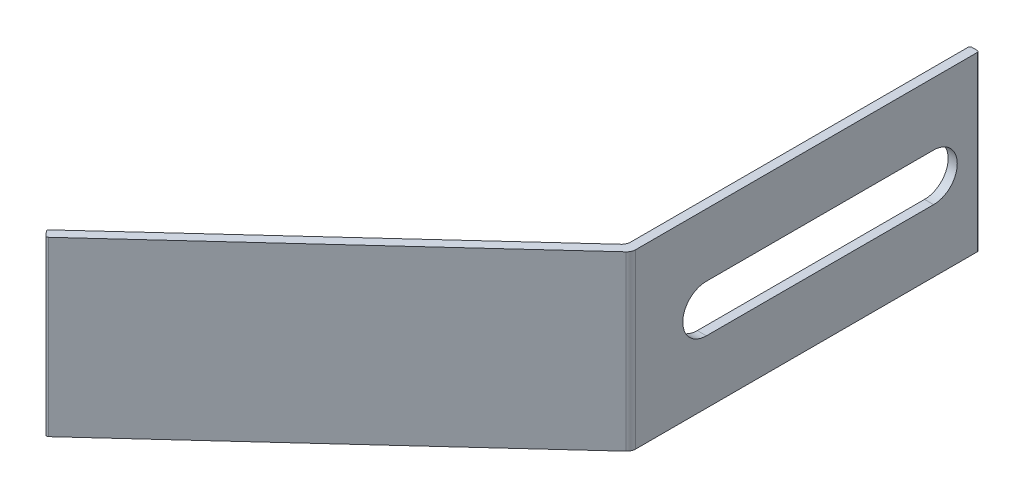
SolidWorks part; units mm, degrees
ref_plane "Front Plane" through (0, 0, 0) normal (0, 0, 1) x (1, 0, 0)
ref_plane "Top Plane" through (0, 0, 0) normal (0, 1, 0) x (1, 0, 0)
ref_plane "Right Plane" through (0, 0, 0) normal (1, 0, 0) x (0, 0, -1)
sketch "Sketch1" plane through (0, 0, 0) normal (0, 1, 0) x (1, 0, 0)
  line L0 (0, 0) -> (0, -38)
  line L1 (0, -38) -> (-33.4724, -68.6718)
  dimension "D1" = 47.5
  dimension "D2" = 45.4
  dimension "D3" = 38
extrude "Extrude-Thin1" add sketch "Sketch1" along normal mid plane 19 thin thin type mid plane wall 1
fillet "Fillet1" radius 1 2 edges at (-0.5, 0, 37.78) (0.5, 0, 38.22)
fillet "Fillet2" radius 0.2 4 edges at (-33.1346, 0, 69.0404) (-33.8102, 0, 68.3032) (0.5, 0, 0) (-0.5, 0, 0)
sketch "Sketch2" plane through (-0.5, 0, 0) normal (-1, 0, 0) x (0, 0, 1)
  line L0 (5, 2.6) -> (30, 2.6)
  line L1 (30, -2.6) -> (5, -2.6)
  arc A0 (30, 2.6) -> (30, -2.6) centre (30, 0) cw
  arc A1 (5, -2.6) -> (5, 2.6) centre (5, 0) cw
  dimension "D1" = 5.2
  dimension "D2" = 25
  dimension "D3" = 5
extrude "Cut-Extrude1" cut sketch "Sketch2" against normal through all
